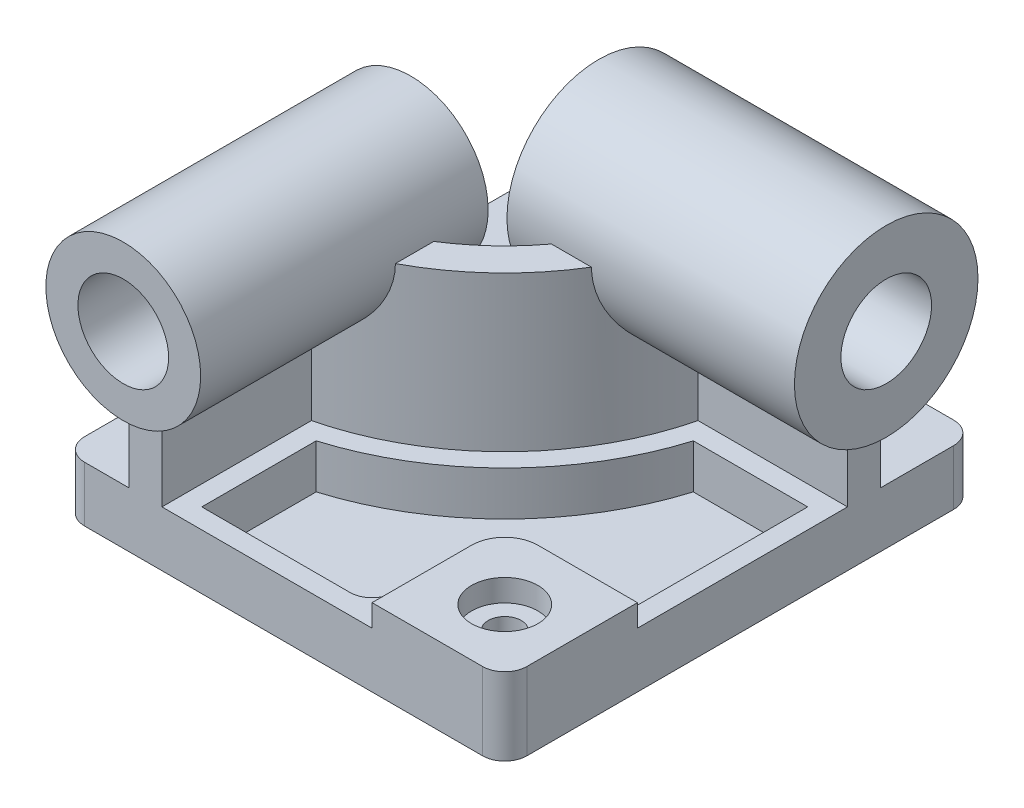
SolidWorks part; units mm, degrees
ref_plane "Front Plane" through (0, 0, 0) normal (0, 0, 1) x (1, 0, 0)
ref_plane "Top Plane" through (0, 0, 0) normal (0, 1, 0) x (1, 0, 0)
ref_plane "Right Plane" through (0, 0, 0) normal (1, 0, 0) x (0, 0, -1)
sketch "Sketch1" plane through (0, 0, 0) normal (0, 1, 0) x (1, 0, 0)
  line L1 (-100, -106.5) -> (100, -106.5)
  line L2 (-100, -106.5) -> (-100, 106.5)
  line L3 (-100, 106.5) -> (100, 106.5)
  line L4 (100, -106.5) -> (100, 106.5)
  line L5 (0, 106.5) -> (0, -106.5) construction
  line L6 (-100, 0) -> (100, 0) construction
  point P0 (0, 0)
  dimension "D1" = 200
  dimension "D2" = 213
extrude "Boss-Extrude1" add sketch "Sketch1" along normal mid plane 25
fillet "Fillet1" radius 10 4 edges at (-100, 0, -106.5) (100, 0, -106.5) (100, 0, 106.5) (-100, 0, 106.5)
sketch "Sketch2" plane through (0, 12.5, 0) normal (0, 1, 0) x (1, 0, 0)
  line L0 (-55, -106.5) -> (-70, -106.5)
  line L1 (-70, -106.5) -> (-70, -26.5)
  line L2 (20, 63.5) -> (100, 63.5)
  line L3 (100, -96.5) -> (100, 96.5) construction
  line L4 (-70, -106.5) -> (-70, -26.5)
  line L5 (100, 63.5) -> (20, 63.5)
  line L6 (-55, -106.5) -> (-55, -38.9284)
  line L7 (100, 63.5) -> (100, 48.5)
  line L8 (32.4284, 48.5) -> (100, 48.5)
  line L9 (20, 48.5) -> (100, 48.5) construction
  line L10 (-55, -106.5) -> (-55, -26.5) construction
  line L11 (100, 63.5) -> (100, 48.5)
  line L12 (-90, -106.5) -> (90, -106.5) construction
  arc A0 (-70, -26.5) -> (20, 63.5) centre (-83.4604, 76.9604) ccw
  arc A1 (-55, -38.9284) -> (32.4284, 48.5) centre (-83.4604, 76.9604) ccw
  arc A2 (-68.0648, -41.3746) -> (34.8746, 61.5648) centre (-83.4604, 76.9604) ccw construction
  point P0 (-62.5, -106.5)
  line M8 (-90, -106.5) -> (90, -106.5)
  line M10 (100, -96.5) -> (100, 96.5)
  dimension "D1" = 15
  dimension "D2" = 15
  dimension "D3" = 80
  dimension "D4" = 80
extrude "Boss-Extrude2" add sketch "Sketch2" along normal blind 70 contours L6 A1 L8 L2 A0 L1 M10 M8
sketch "Sketch3" plane through (0, 12.5, 0) normal (0, 1, 0) x (1, 0, 0)
  line L2 (100, -106.5) -> (100, -124.6448) construction
  line L3 (100, -96.5) -> (100, 48.5) construction
  line L5 (100, -46.5) -> (55, -46.5)
  line L6 (40, -61.5) -> (40, -106.5)
  line L8 (100, -106.5) -> (119.5631, -106.5) construction
  line L9 (40, -106.5) -> (90, -106.5)
  line L10 (100, -96.5) -> (100, -46.5)
  arc A0 (55, -46.5) -> (40, -61.5) centre (55, -61.5) ccw
  arc A2 (90, -106.5) -> (100, -96.5) centre (90, -96.5) ccw
  dimension "D1" = 15
extrude "Boss-Extrude3" add sketch "Sketch3" along normal blind 10
sketch "Sketch4" plane through (0, 12.5, 0) normal (0, 1, 0) x (1, 0, 0)
  line L0 (-55, -106.5) -> (-55, -38.9284)
  line L1 (100, 48.5) -> (32.4284, 48.5)
  line L2 (-46, -97.5) -> (-46, -45.7829)
  line L3 (91, 39.5) -> (39.2829, 39.5)
  line L8 (100, -37.5) -> (55, -37.5)
  line L9 (31, -61.5) -> (31, -106.5)
  line L10 (91, -37.5) -> (55, -37.5)
  line L11 (31, -61.5) -> (31, -87.5)
  line L14 (100, 39.5) -> (39.2829, 39.5) construction
  line L15 (-46, -97.5) -> (21, -97.5)
  line L17 (91, 39.5) -> (91, -37.5)
  line L18 (-46, -106.5) -> (-46, -45.7829) construction
  arc A0 (-55, -38.9284) -> (32.4284, 48.5) centre (-83.4604, 76.9604) ccw
  arc A1 (-46, -45.7829) -> (39.2829, 39.5) centre (-83.4604, 76.9604) ccw
  arc A3 (21, -97.5) -> (31, -87.5) centre (21, -87.5) ccw
  arc A4 (55, -37.5) -> (31, -61.5) centre (55, -61.5) ccw
  arc A5 (55, -37.5) -> (31, -61.5) centre (55, -61.5) ccw
  dimension "D1" = 9
  dimension "D3" = 10
  dimension "D2" = 9
extrude "Cut-Extrude1" cut sketch "Sketch4" against normal blind 20 contours L15 A3 L11 A5 L10 L17 L3 A1 L2
sketch "Sketch5" plane through (0, 22.5, 0) normal (0, 1, 0) x (1, 0, 0)
  line L0 (44.3934, -50.8934) -> (97.0711, -103.5711) construction
  arc A0 (55, -46.5) -> (40, -61.5) centre (55, -61.5) ccw construction
  arc A1 (90, -106.5) -> (100, -96.5) centre (90, -96.5) ccw construction
  circle A2 centre (70.7322, -77.2322) radius 15
  circle A3 centre (70.7322, -77.2322) radius 7.5
extrude "Cut-Extrude2" cut sketch "Sketch5" against normal blind 20 contours A3
sketch "Sketch6" plane through (0, 22.5, 0) normal (0, 1, 0) x (1, 0, 0)
  circle A0 centre (70.7322, -77.2322) radius 15
extrude "Cut-Extrude3" cut sketch "Sketch6" against normal blind 10
ref_plane "Plane1" through (0, 0, 106.5) normal (0, 0, 1) x (1, 0, 0)
sketch "Sketch8" plane through (0, 0, 106.5) normal (0, 0, 1) x (1, 0, 0)
  line L0 (-70, 82.5) -> (-55, 82.5) construction
  line L1 (-90, -12.5) -> (90, -12.5) construction
  circle A0 centre (-62.5, 82.5) radius 35
  dimension "D1" = 70
  dimension "D2" = 95
extrude "Boss-Extrude4" add sketch "Sketch8" along normal blind 10 and the other way blind 120
sketch "Sketch9" plane through (0, 0, 116.5) normal (0, 0, 1) x (1, 0, 0)
  circle A0 centre (-62.5, 82.5) radius 20.5
extrude "Cut-Extrude4" cut sketch "Sketch9" against normal through all
ref_plane "Plane2" through (100, 0, 0) normal (1, 0, 0) x (0, 0, -1)
sketch "Sketch10" plane through (100, 0, 0) normal (1, 0, 0) x (0, 0, -1)
  line L0 (48.5, 82.5) -> (63.5, 82.5) construction
  circle A0 centre (56, 82.5) radius 41.5
  circle A1 centre (56, 82.5) radius 20.5
extrude "Boss-Extrude5" add sketch "Sketch10" along normal blind 10 and the other way blind 120
sketch "Sketch11" plane through (100, 0, 0) normal (1, 0, 0) x (0, 0, -1)
  line L0 (48.5, 82.5) -> (63.5, 82.5) construction
  circle A0 centre (56, 82.5) radius 20.5
extrude "Cut-Extrude5" cut sketch "Sketch11" against normal through all
